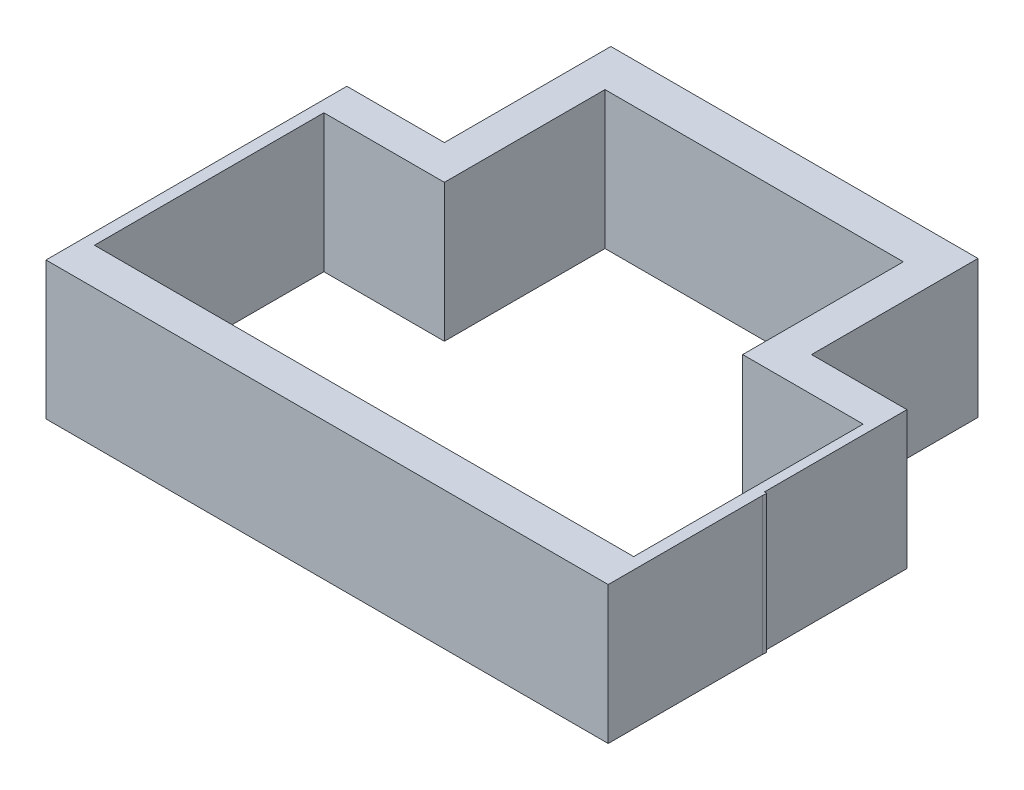
SolidWorks part; units mm, degrees
ref_plane "Front Plane" through (0, 0, 0) normal (0, 0, 1) x (1, 0, 0)
ref_plane "Top Plane" through (0, 0, 0) normal (0, 1, 0) x (1, 0, 0)
ref_plane "Right Plane" through (0, 0, 0) normal (1, 0, 0) x (0, 0, -1)
sketch "Sketch1" plane through (0, 0, 0) normal (0, 1, 0) x (1, 0, 0)
  line L1 (-15.6037, -1.1442) -> (7.8963, -1.1442)
  line L2 (-15.6037, -1.1442) -> (-15.6037, 8.8558)
  line L3 (-15.6037, 8.8558) -> (7.8963, 8.8558)
  line L4 (7.8963, -1.1442) -> (7.8963, 8.8558)
  line L5 (-16.1037, 10.3558) -> (8.3963, 10.3558)
  line L6 (-16.1037, 10.3558) -> (-16.1037, -2.7547)
  line L7 (-16.1037, -2.7547) -> (8.3963, -2.7547)
  line L8 (8.3963, 10.3558) -> (8.3963, -2.7547)
  dimension "D1" = 23.5
  dimension "D2" = 10
  dimension "D3" = 1.5
  dimension "D4" = 0.5
  dimension "D5" = 0.5
extrude "Boss-Extrude1" add sketch "Sketch1" along normal blind 6
sketch "Sketch2" plane through (0, 6, 0) normal (0, 1, 0) x (1, 0, 0)
  line L0 (7.8963, 8.8558) -> (-15.6037, 8.8558) construction
  line L1 (-10.3537, 15.8558) -> (2.6463, 15.8558)
  line L2 (-10.3537, 15.8558) -> (-10.3537, 8.8558)
  line L3 (-10.3537, 8.8558) -> (2.6463, 8.8558)
  line L4 (2.6463, 15.8558) -> (2.6463, 8.8558)
  line L6 (-11.8537, 17.6101) -> (4.1463, 17.6101)
  line L7 (-11.8537, 17.6101) -> (-11.8537, 8.8558)
  line L8 (-11.8537, 8.8558) -> (4.1463, 8.8558)
  line L9 (4.1463, 17.6101) -> (4.1463, 8.8558)
  line L11 (8.3963, -2.7547) -> (8.3963, 10.3558) construction
  line M12 (8.3963, 10.3558) -> (-16.1037, 10.3558)
  dimension "D1" = 13
  dimension "D2" = 7
  dimension "D3" = 5.75
  dimension "D4" = 1.5
  dimension "D5" = 1.5
extrude "Boss-Extrude2" add sketch "Sketch2" against normal up to surface (6 mm away) contours L9 L6 L7 L2 L1 L4 M12 up to face at (-3.8537, 0, -3.8005)
sketch "Sketch3" plane through (0, 6, 0) normal (0, 1, 0) x (1, 0, 0)
  line L0 (-10.3537, 15.8558) -> (-10.3537, 10.3558) construction
  line L1 (-10.3537, 11.3652) -> (3.629, 11.3652)
  line L2 (-10.3537, 11.3652) -> (-10.3537, 6.9274)
  line L3 (-10.3537, 6.9274) -> (3.629, 6.9274)
  line L4 (3.629, 11.3652) -> (3.629, 6.9274)
extrude "Cut-Extrude1" cut sketch "Sketch3" against normal blind 11
sketch "Sketch4" plane through (0, 6, 0) normal (0, 1, 0) x (1, 0, 0)
  line L1 (2.6463, 11.3652) -> (3.629, 11.3652)
  line L2 (2.6463, 11.3652) -> (2.6463, 8.8558)
  line L3 (2.6463, 8.8558) -> (3.629, 8.8558)
  line L4 (3.629, 11.3652) -> (3.629, 8.8558)
extrude "Boss-Extrude3" add sketch "Sketch4" against normal up to surface (6 mm away) up to face at (-3.8537, 0, -8.8917)
sketch "Sketch5" plane through (8.3963, 0, 0) normal (1, 0, 0) x (0, 0, -1)
  line L0 (-2.7547, 0) -> (10.3558, 0) construction
  line L1 (10.3558, 6) -> (5.4635, 6)
  line L2 (10.3558, 6) -> (10.3558, 0)
  line L3 (10.3558, 0) -> (5.4635, 0)
  line L4 (5.4635, 6) -> (5.4635, 0)
extrude "Boss-Extrude4" add sketch "Sketch5" along normal up to surface (3.3 mm away)
fillet "Fillet1" radius 1.5 1 edges at (8.3963, 3, -5.4635)
sketch "Sketch6" plane through (0, 6, 0) normal (0, 1, 0) x (1, 0, 0)
  line L1 (8.3034, 4.143) -> (12.286, 4.143)
  line L2 (8.3034, 4.143) -> (8.3034, 10.9478)
  line L3 (8.3034, 10.9478) -> (12.286, 10.9478)
  line L4 (12.286, 4.143) -> (12.286, 10.9478)
extrude "Cut-Extrude2" cut sketch "Sketch6" against normal blind 10
